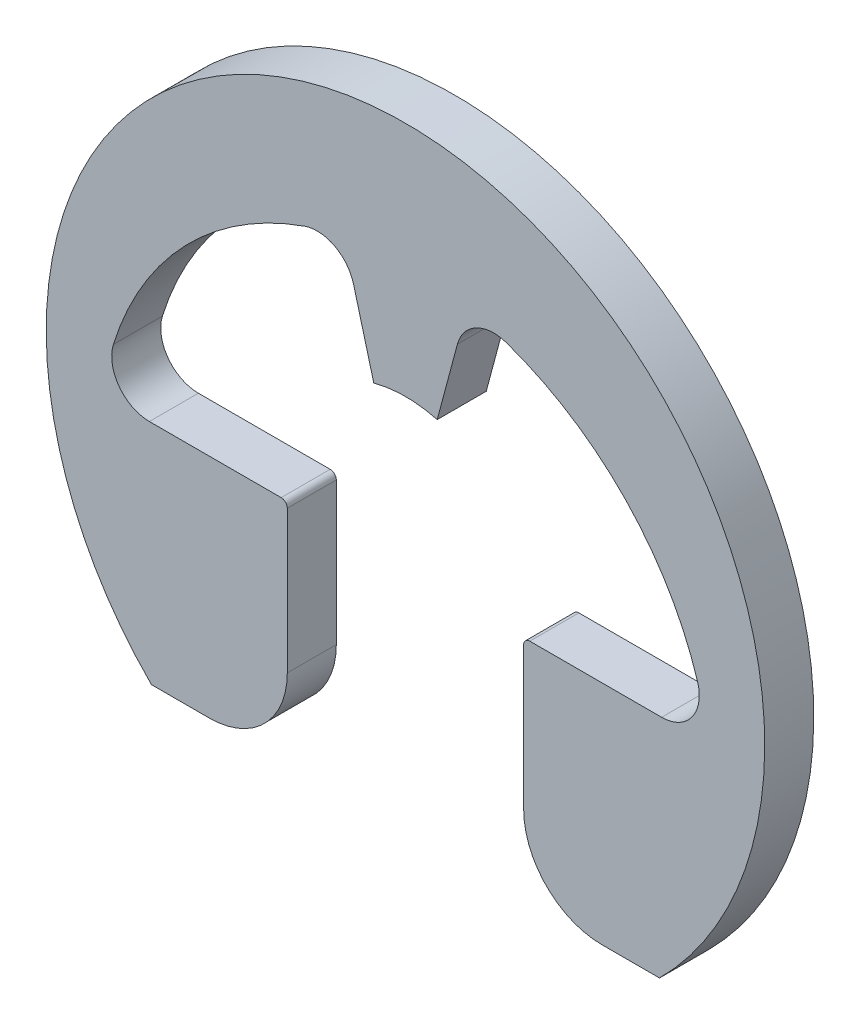
SolidWorks part; units mm, degrees
ref_plane "Plane1" through (0, 0, 0) normal (0, 0, 1) x (1, 0, 0)
ref_plane "Plane2" through (0, 0, 0) normal (0, 1, 0) x (1, 0, 0)
ref_plane "Plane3" through (0, 0, 0) normal (1, 0, 0) x (0, 0, -1)
sketch "Clipboard" plane through (0, 0, 0) normal (0, 0, 1) x (1, 0, 0)
  line L0 (0, 0) -> (1.5, 0)
  circle A0 centre (0, 0) radius 1.45
  circle A1 centre (0, 0) radius 4.25
  dimension "FreeID" = 2.9
  dimension "FreeOD" = 8.5
  dimension "LargeSection" = 1.5
sketch "BodySke" plane through (0, 0, 0) normal (0, 0, 1) x (1, 0, 0)
  line L0 (-3.6466, 0) -> (3.6466, 0) construction
  line L1 (0, 0) -> (0, 2.8966) construction
  line L2 (0, 0) -> (0.1962, 0.7323) construction
  line L3 (0, 0) -> (4.2467, -1.1379) construction
  line L4 (0, 0) -> (-0.1962, 0.7323) construction
  line L5 (0, 0) -> (-4.2467, -1.1379) construction
  line L6 (0, 0) -> (3.1088, -3.1088) construction
  line L7 (0, 0) -> (-3.1088, -3.1088) construction
  line L8 (3.1088, -3.1088) -> (2.4022, -3.1088)
  line L9 (-2.4022, -3.1088) -> (-3.1088, -3.1088)
  line L10 (1.5213, -0.3326) -> (3.1346, -0.3326)
  line L11 (0.6356, 2.372) -> (0.3882, 1.4489)
  line L12 (-0.6356, 2.372) -> (-0.3882, 1.4489)
  line L13 (1.4463, -0.4076) -> (1.4463, -2.153)
  line L14 (-1.5213, -0.3326) -> (-3.1346, -0.3326)
  line L15 (-1.4463, -0.4076) -> (-1.4463, -2.153)
  circle A0 centre (0, 0) radius 1.5 construction
  arc A1 (3.6466, 0) -> (-3.6466, 0) centre (0, -0.8471) ccw construction
  arc A2 (3.1088, -3.1088) -> (-3.1088, -3.1088) centre (0, 0) ccw
  arc A3 (1.5213, -0.3326) -> (1.4463, -0.4076) centre (1.5213, -0.4076) ccw
  arc A4 (-1.4463, -0.4076) -> (-1.5213, -0.3326) centre (-1.5213, -0.4076) ccw
  arc A5 (-3.5746, 0.2651) -> (-1.2324, 2.6879) centre (0, -0.8471) cw
  arc A6 (-0.3882, 1.4489) -> (0.3882, 1.4489) centre (0, 0) cw
  arc A7 (1.2324, 2.6879) -> (3.5746, 0.2651) centre (0, -0.8471) cw
  arc A8 (3.1346, -0.3326) -> (3.5746, 0.2651) centre (3.1346, 0.1282) ccw
  arc A9 (1.2324, 2.6879) -> (0.6356, 2.372) centre (1.0807, 2.2527) ccw
  arc A10 (-0.6356, 2.372) -> (-1.2324, 2.6879) centre (-1.0807, 2.2527) ccw
  arc A11 (-3.5746, 0.2651) -> (-3.1346, -0.3326) centre (-3.1346, 0.1282) ccw
  arc A12 (1.4463, -2.153) -> (2.4022, -3.1088) centre (2.4022, -2.153) ccw
  arc A13 (-2.4022, -3.1088) -> (-1.4463, -2.153) centre (-2.4022, -2.153) ccw
  dimension "D1" = 15
  dimension "GrooveDia" = 3
  dimension "OutsideDia" = 8.7931
  dimension "D3" = 30
  dimension "CavityFilletRad" = 0.4609
  dimension "InnerTipRad" = 0.075
  dimension "OuterTipRadius" = 0.9559
  dimension "CavityWidth" = 7.2931
  dimension "CavityHeight" = 2.8966
extrude "Body" add sketch "BodySke" against normal blind 0.6
equation "' \"FreeID@Clipboard\" = 2.9"
equation "' \"Thickness@Body\" = 0.6"
equation "' \"GrooveDia@BodySke\" = 3.0"
equation "' \"FreeOD@Clipboard\" = 8.5"
equation "' \"LargeSection@Clipboard\" = 1.5"
equation "' \"FreeID@Clipboard\" = 11.5"
equation "' \"Thickness@Body\" = 1.1"
equation "' \"GrooveDia@BodySke\" = 11.8"
equation "' \"FreeOD@Clipboard\" = 23.2"
equation "' \"LargeSection@Clipboard\" = 3.9"
equation "\"OutsideDia@BodySke\" = ( \"GrooveDia@BodySke\"  /  \"FreeID@Clipboard\" )  * \"FreeOD@Clipboard\""
equation "\"CavityHeight@BodySke\" = \"OutsideDia@BodySke\"  /  2 - \"LargeSection@Clipboard\""
equation "\"CavityWidth@BodySke\" = \"OutsideDia@BodySke\" -  \"LargeSection@Clipboard\""
equation "\"CavityFilletRad@BodySke\" =  (\"CavityHeight@BodySke\" * 2 - \"GrooveDia@BodySke\") / 2 * 0.33"
equation "\"InnerTipRad@BodySke\" = \"GrooveDia@BodySke\" * 0.025"
equation "\"OuterTipRadius@BodySke\" =  (\"OutsideDia@BodySke\" - \"GrooveDia@BodySke\") / 2 * 0.33"
